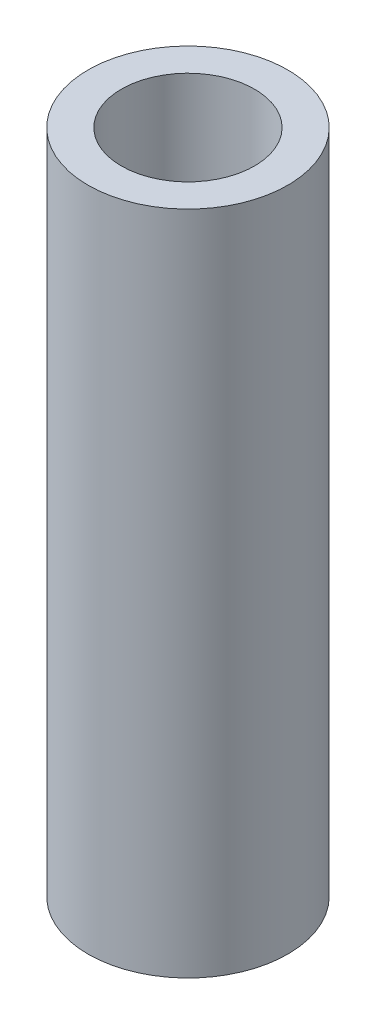
SolidWorks part; units mm, degrees
ref_plane "Front Plane" through (0, 0, 0) normal (0, 0, 1) x (1, 0, 0)
ref_plane "Top Plane" through (0, 0, 0) normal (0, 1, 0) x (1, 0, 0)
ref_plane "Right Plane" through (0, 0, 0) normal (1, 0, 0) x (0, 0, -1)
sketch "Sketch1" plane through (0, 0, 0) normal (0, 1, 0) x (1, 0, 0)
  circle A0 centre (0, 0) radius 3
  dimension "D1" = 6
extrude "Boss-Extrude1" add sketch "Sketch1" along normal blind 20
sketch "Sketch2" plane through (0, 20, 0) normal (0, 1, 0) x (1, 0, 0)
  circle A0 centre (0, 0) radius 2
  dimension "D1" = 4
extrude "Cut-Extrude1" cut sketch "Sketch2" against normal through all
